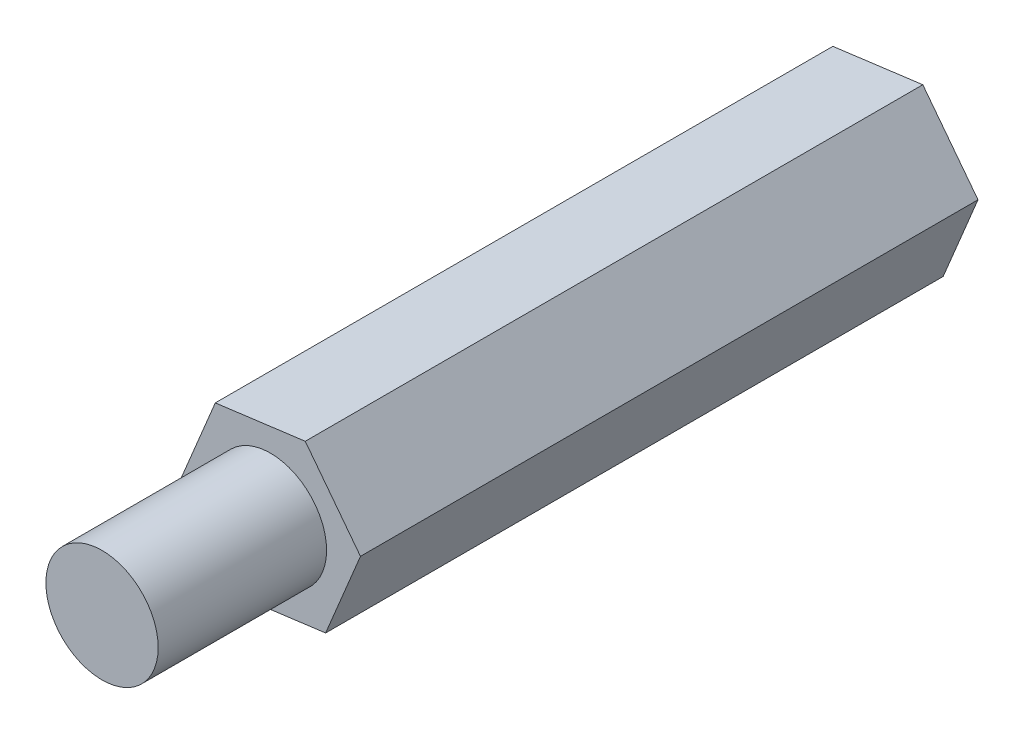
SolidWorks part; units mm, degrees
ref_plane "前视基准面" through (0, 0, 0) normal (0, 0, 1) x (1, 0, 0)
ref_plane "上视基准面" through (0, 0, 0) normal (0, 1, 0) x (1, 0, 0)
ref_plane "右视基准面" through (0, 0, 0) normal (1, 0, 0) x (0, 0, -1)
sketch "草图1" plane through (0, 0, 0) normal (0, 0, 1) x (1, 0, 0)
  line L1 (0.9829, -1.2835) -> (1.603, 0.2094)
  line L2 (1.603, 0.2094) -> (0.6201, 1.4929)
  line L3 (0.6201, 1.4929) -> (-0.9829, 1.2835)
  line L4 (-0.9829, 1.2835) -> (-1.603, -0.2094)
  line L5 (-1.603, -0.2094) -> (-0.6201, -1.4929)
  line L6 (-0.6201, -1.4929) -> (0.9829, -1.2835)
  circle A0 centre (0, 0) radius 1.4 construction
  dimension "D1" = 2.8
extrude "凸台-拉伸1" add sketch "草图1" along normal blind 11
sketch "草图2" plane through (0, 0, 11) normal (0, 0, 1) x (1, 0, 0)
  line L6 (-0.6201, -1.4929) -> (0.9829, -1.2835)
  line L7 (0.9829, -1.2835) -> (1.603, 0.2094)
  line L8 (1.603, 0.2094) -> (0.6201, 1.4929)
  line L9 (0.6201, 1.4929) -> (-0.9829, 1.2835)
  line L10 (-0.9829, 1.2835) -> (-1.603, -0.2094)
  line L11 (-1.603, -0.2094) -> (-0.6201, -1.4929)
  line L12 (-0.6201, -1.4929) -> (0.9829, -1.2835)
  line L13 (0.9829, -1.2835) -> (1.603, 0.2094)
  line L14 (1.603, 0.2094) -> (0.6201, 1.4929)
  line L15 (0.6201, 1.4929) -> (-0.9829, 1.2835)
  line L16 (-0.9829, 1.2835) -> (-1.603, -0.2094)
  line L17 (-1.603, -0.2094) -> (-0.6201, -1.4929)
  circle A0 centre (0, 0) radius 1
  dimension "D2" = 2
  dimension "D1" = 0
extrude "凸台-拉伸2" add sketch "草图2" along normal blind 3 contours A0
sketch "草图3" plane through (0, 0, 0) normal (0, 0, -1) x (-1, 0, 0)
  line L6 (-0.9829, -1.2835) -> (0.6201, -1.4929)
  line L7 (0.6201, -1.4929) -> (1.603, -0.2094)
  line L8 (1.603, -0.2094) -> (0.9829, 1.2835)
  line L9 (0.9829, 1.2835) -> (-0.6201, 1.4929)
  line L10 (-0.6201, 1.4929) -> (-1.603, 0.2094)
  line L11 (-1.603, 0.2094) -> (-0.9829, -1.2835)
  line L12 (-0.9829, -1.2835) -> (0.6201, -1.4929)
  line L13 (0.6201, -1.4929) -> (1.603, -0.2094)
  line L14 (1.603, -0.2094) -> (0.9829, 1.2835)
  line L15 (0.9829, 1.2835) -> (-0.6201, 1.4929)
  line L16 (-0.6201, 1.4929) -> (-1.603, 0.2094)
  line L17 (-1.603, 0.2094) -> (-0.9829, -1.2835)
  circle A0 centre (0, 0) radius 1
  dimension "D2" = 2
  dimension "D1" = 0
extrude "切除-拉伸1" cut sketch "草图3" against normal blind 3 contours A0
